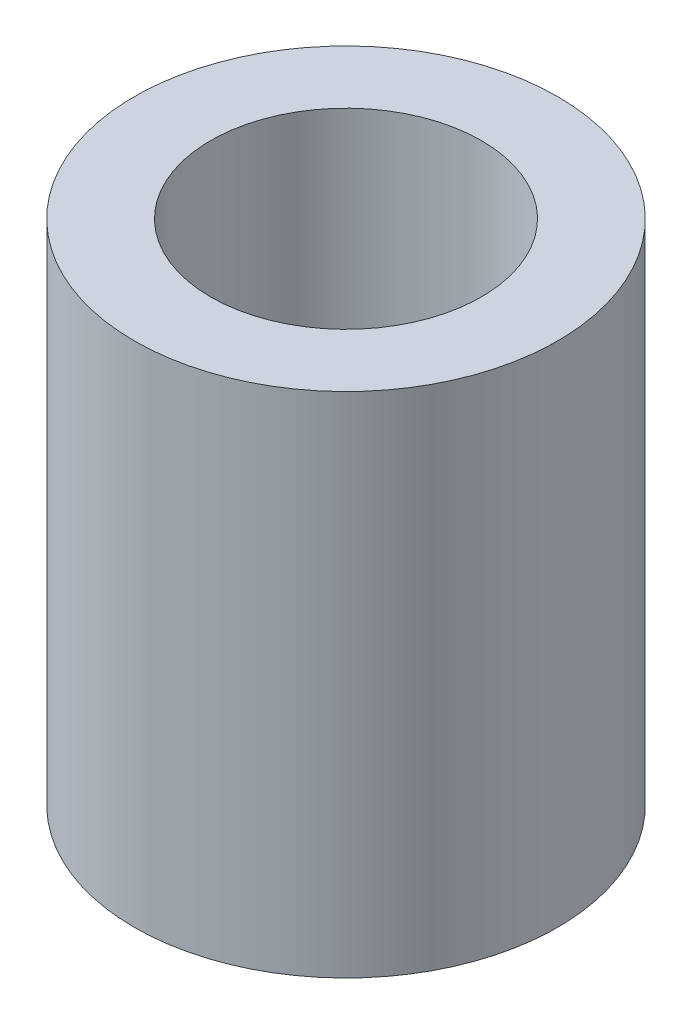
SolidWorks part; units mm, degrees
ref_plane "Спереди" through (0, 0, 0) normal (0, 0, 1) x (1, 0, 0)
ref_plane "Сверху" through (0, 0, 0) normal (0, 1, 0) x (1, 0, 0)
ref_plane "Справа" through (0, 0, 0) normal (1, 0, 0) x (0, 0, -1)
other "Configuration Table"
sketch "Sketch1" plane through (0, 0, 0) normal (0, 1, 0) x (1, 0, 0)
  circle A0 centre (0, 0) radius 1.6
  circle A1 centre (0, 0) radius 2.5
  dimension "D1" = 3.2
  dimension "D2" = 5
extrude "Boss-Extrude1" add sketch "Sketch1" along normal blind 6
